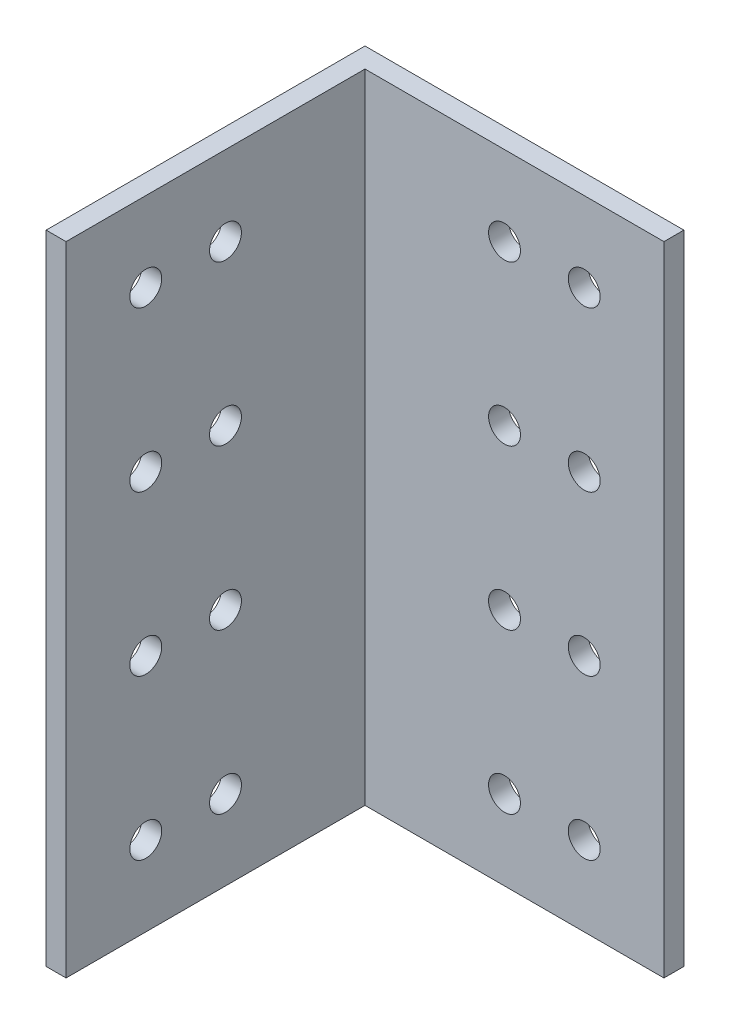
SolidWorks part; units mm, degrees
material "6061-T6 (SS)"
ref_plane "Front Plane" through (0, 0, 0) normal (0, 0, 1) x (1, 0, 0)
ref_plane "Top Plane" through (0, 0, 0) normal (0, 1, 0) x (1, 0, 0)
ref_plane "Right Plane" through (0, 0, 0) normal (1, 0, 0) x (0, 0, -1)
sketch "Sketch2" plane through (0, 0, 0) normal (0, 1, 0) x (1, 0, 0)
  line L1 (-25.4, -25.4) -> (25.4, -25.4)
  line L2 (-25.4, -25.4) -> (-25.4, 25.4)
  line L3 (-25.4, 25.4) -> (25.4, 25.4)
  line L4 (25.4, -25.4) -> (25.4, 25.4)
  line L5 (-25.4, -25.4) -> (25.4, 25.4) construction
  line L6 (-25.4, 25.4) -> (25.4, -25.4) construction
  line L7 (-22.225, 22.225) -> (25.4, 22.225)
  line L8 (-22.225, 22.225) -> (-22.225, -25.4)
  line L9 (-22.225, -25.4) -> (25.4, -25.4)
  line L10 (25.4, 22.225) -> (25.4, -25.4)
  point P0 (0, 0)
  dimension "D1" = 50.8
  dimension "D2" = 50.8
  dimension "D3" = 47.625
  dimension "D4" = 47.625
extrude "Boss-Extrude1" add sketch "Sketch2" along normal blind 101.6 contours L8 L7 L4 L3 L2 L1
sketch "Sketch3" plane through (0, 0, -22.225) normal (0, 0, 1) x (1, 0, 0)
  line L0 (-22.225, 0) -> (25.4, 0) construction
  line L2 (25.4, 101.6) -> (25.4, 0) construction
  circle A0 centre (12.7, 88.9) radius 2.54
  circle A1 centre (0, 88.9) radius 2.54
  circle A2 centre (0, 63.5) radius 2.54
  circle A3 centre (12.7, 63.5) radius 2.54
  circle A4 centre (0, 38.1) radius 2.54
  circle A5 centre (12.7, 38.1) radius 2.54
  circle A6 centre (0, 12.7) radius 2.54
  circle A7 centre (12.7, 12.7) radius 2.54
  point P16 (0, 0)
  point P17 (0, 0)
  point P18 (0, 0)
  point P19 (0, 0)
  point P20 (0, 0)
  point P21 (0, 0)
  point P22 (0, 0)
  point P27 (19.8157, 76.9251)
  dimension "D1" = 5.08
  dimension "D7" = 12.7
  dimension "D2" = 12.7
  dimension "D3" = 12.7
  dimension "D4" = 25.4
  dimension "D5" = 25.4
  dimension "D6" = 25.4
extrude "Cut-Extrude1" cut sketch "Sketch3" against normal through all
sketch "Sketch4" plane through (-22.225, 0, 0) normal (1, 0, 0) x (0, 0, -1)
  line L0 (-25.4, 101.6) -> (-25.4, 0) construction
  line L1 (22.225, 0) -> (-25.4, 0) construction
  circle A0 centre (-12.7, 88.9) radius 2.54
  circle A1 centre (0, 88.9) radius 2.54
  circle A2 centre (-12.7, 63.5) radius 2.54
  circle A3 centre (0, 63.5) radius 2.54
  circle A4 centre (-12.7, 38.1) radius 2.54
  circle A5 centre (0, 38.1) radius 2.54
  circle A6 centre (-12.7, 12.7) radius 2.54
  circle A7 centre (0, 12.7) radius 2.54
  point P16 (0, 0)
  point P17 (0, 0)
  point P18 (0, 0)
  point P19 (0, 0)
  point P20 (0, 0)
  point P21 (0, 0)
  dimension "D1" = 5.08
  dimension "D2" = 12.7
  dimension "D3" = 12.7
  dimension "D4" = 12.7
  dimension "D5" = 25.4
  dimension "D6" = 25.4
  dimension "D7" = 25.4
extrude "Cut-Extrude2" cut sketch "Sketch4" against normal through all
